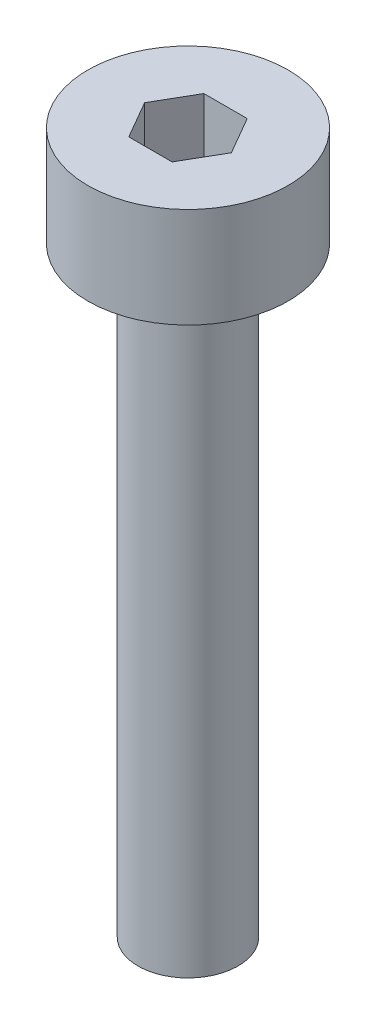
SolidWorks part; units mm, degrees
material "AISI 304"
ref_plane "前视基准面" through (0, 0, 0) normal (0, 0, 1) x (1, 0, 0)
ref_plane "上视基准面" through (0, 0, 0) normal (0, 1, 0) x (1, 0, 0)
ref_plane "右视基准面" through (0, 0, 0) normal (1, 0, 0) x (0, 0, -1)
sketch "草图1" plane through (0, 0, 0) normal (0, 1, 0) x (1, 0, 0)
  circle A0 centre (0, 0) radius 2
  dimension "D1" = 4
extrude "杯头高度" add sketch "草图1" along normal blind 2
sketch "草图2" plane through (0, 2, 0) normal (0, 1, 0) x (1, 0, 0)
  line L1 (0.866, 0) -> (0.433, 0.75)
  line L2 (0.433, 0.75) -> (-0.433, 0.75)
  line L3 (-0.433, 0.75) -> (-0.866, 0)
  line L4 (-0.866, 0) -> (-0.433, -0.75)
  line L5 (-0.433, -0.75) -> (0.433, -0.75)
  line L6 (0.433, -0.75) -> (0.866, 0)
  circle A0 centre (0, 0) radius 0.75 construction
  dimension "D1" = 1.5
extrude "内六角深度" cut sketch "草图2" against normal blind 1.5
sketch "草图3" plane through (0, 0, 0) normal (0, -1, 0) x (1, 0, 0)
  circle A0 centre (0, 0) radius 1
  dimension "D1" = 2
extrude "螺纹长度" add sketch "草图3" along normal blind 12
